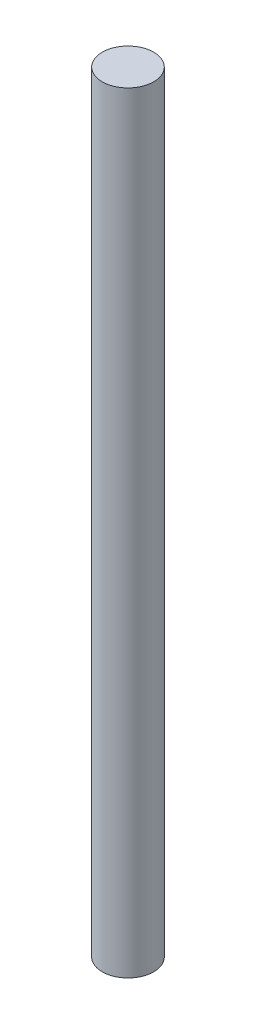
SolidWorks part; units mm, degrees
ref_plane "Front" through (0, 0, 0) normal (0, 0, 1) x (1, 0, 0)
ref_plane "Top" through (0, 0, 0) normal (0, 1, 0) x (1, 0, 0)
ref_plane "Right" through (0, 0, 0) normal (1, 0, 0) x (0, 0, -1)
sketch "Sketch1" plane through (0, 0, 0) normal (0, 1, 0) x (1, 0, 0)
  circle A0 centre (0, 0) radius 5
  dimension "D1" = 10
extrude "Boss-Extrude1" add sketch "Sketch1" along normal blind 150
